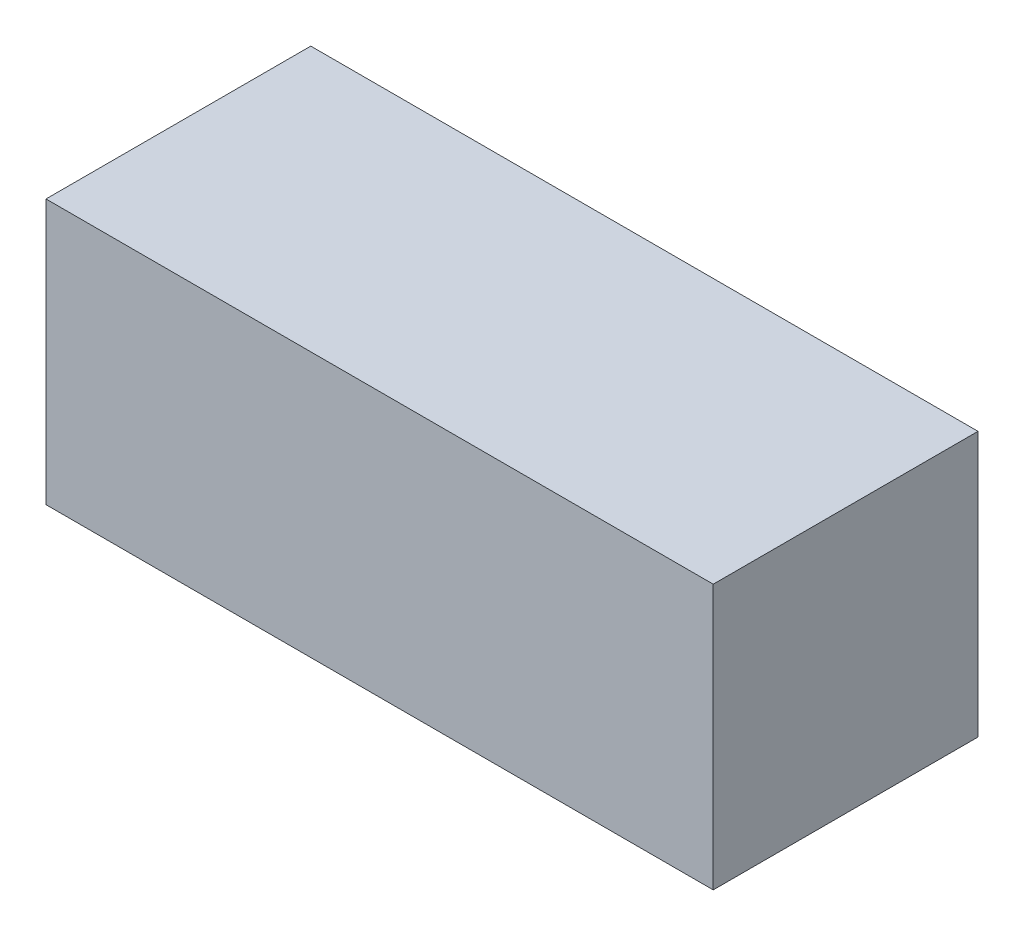
SolidWorks part; units mm, degrees
ref_plane "Front Plane" through (0, 0, 0) normal (0, 0, 1) x (1, 0, 0)
ref_plane "Top Plane" through (0, 0, 0) normal (0, 1, 0) x (1, 0, 0)
ref_plane "Right Plane" through (0, 0, 0) normal (1, 0, 0) x (0, 0, -1)
sketch "Sketch1" plane through (0, 0, 0) normal (0, 1, 0) x (1, 0, 0)
  line L1 (-31.5, -12.5) -> (31.5, -12.5)
  line L2 (-31.5, -12.5) -> (-31.5, 12.5)
  line L3 (-31.5, 12.5) -> (31.5, 12.5)
  line L4 (31.5, -12.5) -> (31.5, 12.5)
  line L5 (-31.5, -12.5) -> (31.5, 12.5) construction
  line L6 (-31.5, 12.5) -> (31.5, -12.5) construction
  point P0 (0, 0)
  dimension "D1" = 63
  dimension "D2" = 25
extrude "Boss-Extrude1" add sketch "Sketch1" along normal blind 25
